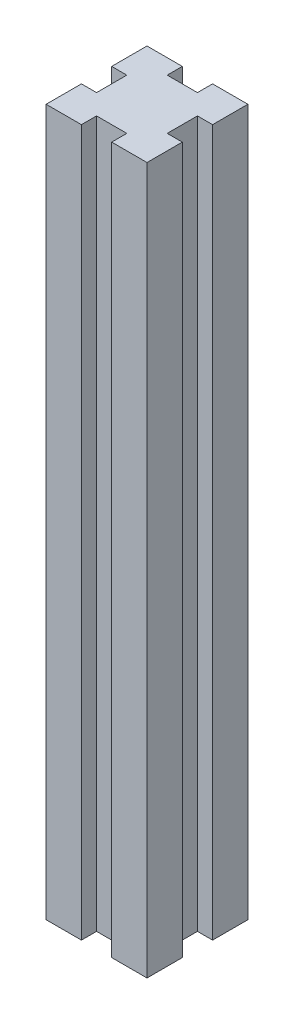
SolidWorks part; units mm, degrees
ref_plane "정면" through (0, 0, 0) normal (0, 0, 1) x (1, 0, 0)
ref_plane "윗면" through (0, 0, 0) normal (0, 1, 0) x (1, 0, 0)
ref_plane "우측면" through (0, 0, 0) normal (1, 0, 0) x (0, 0, -1)
sketch "스케치1" plane through (0, 0, 0) normal (0, 1, 0) x (1, 0, 0)
  line L0 (3, 10) -> (10, 10)
  line L1 (-10, 10) -> (-3, 10)
  line L2 (-10, 10) -> (-10, 3)
  line L3 (-10, -10) -> (-3, -10)
  line L4 (10, 10) -> (10, 3)
  line L5 (-10, -3) -> (-10, -10)
  line L6 (-3, 10) -> (-3, 7)
  line L7 (-3, 7) -> (3, 7)
  line L8 (3, 10) -> (3, 7)
  line L9 (10, 3) -> (7, 3)
  line L10 (3, -10) -> (10, -10)
  line L11 (10, -3) -> (7, -3)
  line L12 (7, 3) -> (7, -3)
  line L14 (3, -10) -> (3, -7)
  line L15 (3, -7) -> (-3, -7)
  line L16 (-3, -10) -> (-3, -7)
  line L17 (-10, -3) -> (-7, -3)
  line L18 (10, -3) -> (10, -10)
  line L19 (-10, 3) -> (-7, 3)
  line L20 (-7, -3) -> (-7, 3)
  point P21 (0, 7)
  point P22 (0, -7)
  point P23 (-7, 0)
  point P24 (7, 0)
  dimension "D1" = 20
  dimension "D2" = 20
  dimension "D3" = 10
  dimension "D4" = 10
  dimension "D5" = 6
  dimension "D6" = 3
extrude "보스-돌출1" add sketch "스케치1" along normal blind 140
